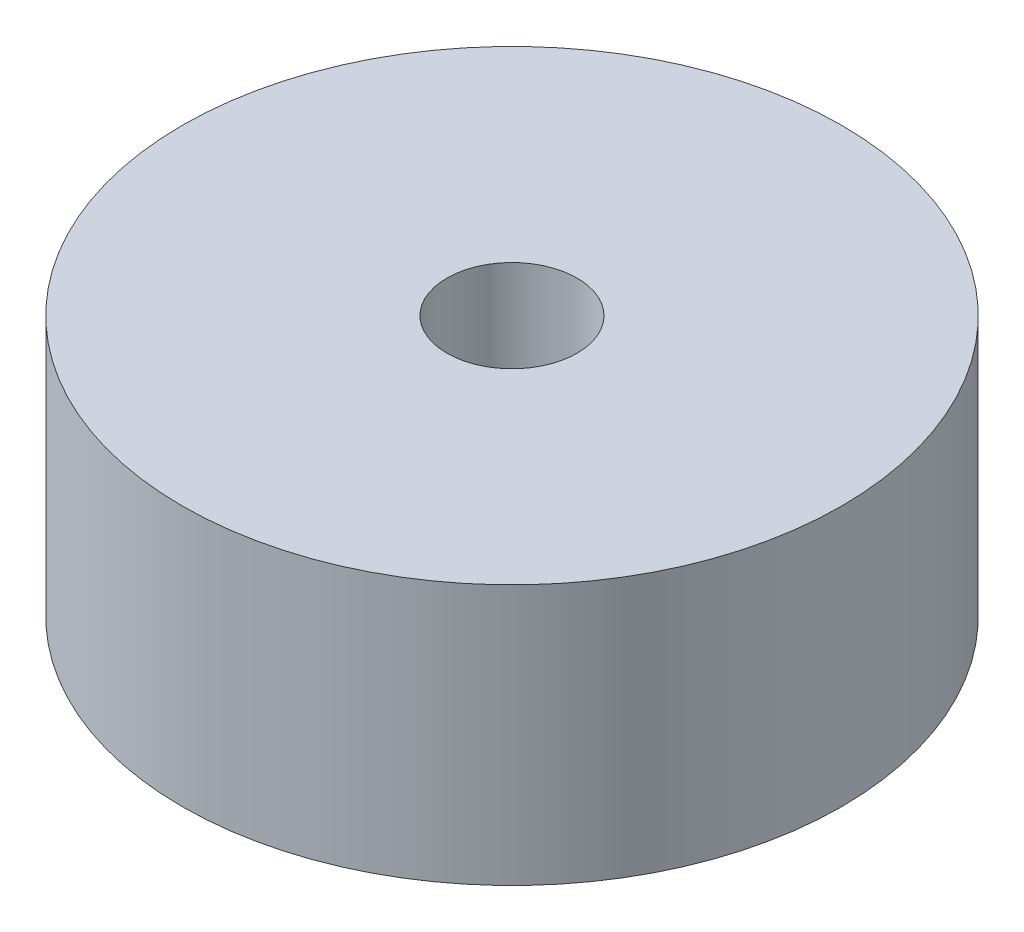
SolidWorks part; units mm, degrees
ref_plane "Front" through (0, 0, 0) normal (0, 0, 1) x (1, 0, 0)
ref_plane "Top" through (0, 0, 0) normal (0, 1, 0) x (1, 0, 0)
ref_plane "Right" through (0, 0, 0) normal (1, 0, 0) x (0, 0, -1)
sketch "Sketch1" plane through (0, 0, 0) normal (0, 1, 0) x (1, 0, 0)
  circle A0 centre (0, 0) radius 7.9375 construction
  circle A1 centre (0, 0) radius 1.6891 construction
  circle A2 centre (0, 0) radius 8.0391
  circle A3 centre (0, 0) radius 1.5875
  dimension "D1" = 15.875
  dimension "D2" = 3.3782
  dimension "D3" = 0.1016
  dimension "D4" = 0.1016
extrude "Boss-Extrude1" add sketch "Sketch1" along normal blind 6.35
